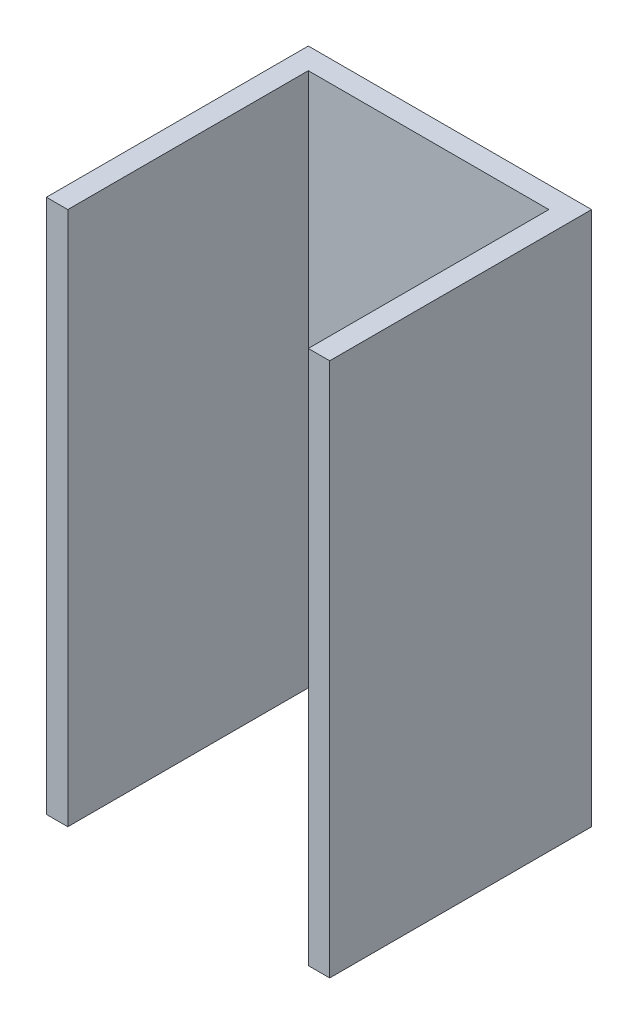
SolidWorks part; units mm, degrees
ref_plane "Front Plane" through (0, 0, 0) normal (0, 0, 1) x (1, 0, 0)
ref_plane "Top Plane" through (0, 0, 0) normal (0, 1, 0) x (1, 0, 0)
ref_plane "Right Plane" through (0, 0, 0) normal (1, 0, 0) x (0, 0, -1)
sketch "Sketch1" plane through (0, 0, 0) normal (0, 1, 0) x (1, 0, 0)
  line L0 (-11.25, 0) -> (11.25, 0)
  line L1 (11.25, 0) -> (11.25, -22.5)
  line L2 (11.25, -22.5) -> (13.25, -22.5)
  line L3 (13.25, -22.5) -> (13.25, 2)
  line L4 (13.25, 2) -> (-13.25, 2)
  line L5 (-13.25, 2) -> (-13.25, -22.5)
  line L6 (-13.25, -22.5) -> (-11.25, -22.5)
  line L7 (-11.25, -22.5) -> (-11.25, 0)
  dimension "D1" = 2
  dimension "D2" = 22.5
  dimension "D3" = 22.5
  dimension "D4" = 2
extrude "Boss-Extrude1" add sketch "Sketch1" along normal blind 50
